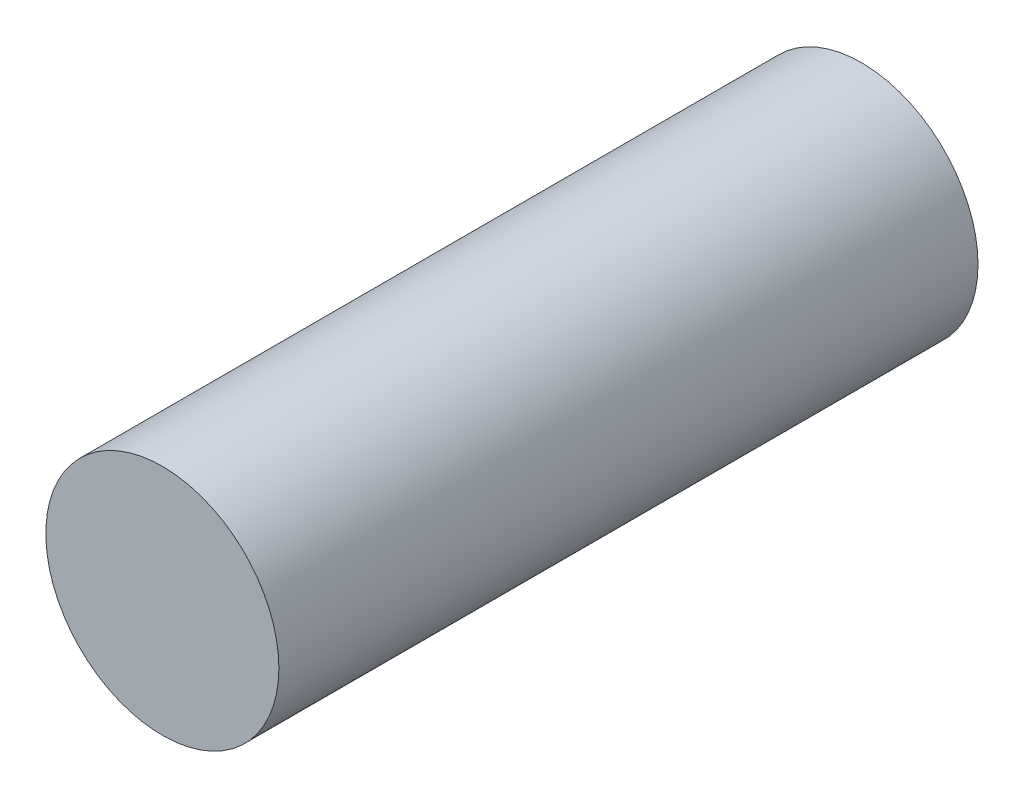
SolidWorks part; units mm, degrees
material "7075-T6 (SN)"
ref_plane "Front Plane" through (0, 0, 0) normal (0, 0, 1) x (1, 0, 0)
ref_plane "Top Plane" through (0, 0, 0) normal (0, 1, 0) x (1, 0, 0)
ref_plane "Right Plane" through (0, 0, 0) normal (1, 0, 0) x (0, 0, -1)
sketch "Sketch1" plane through (0, 0, 0) normal (0, 0, 1) x (1, 0, 0)
  circle A0 centre (0, 0) radius 25.4
  dimension "D1" = 50.8
extrude "Boss-Extrude1" add sketch "Sketch1" along normal blind 152.4
